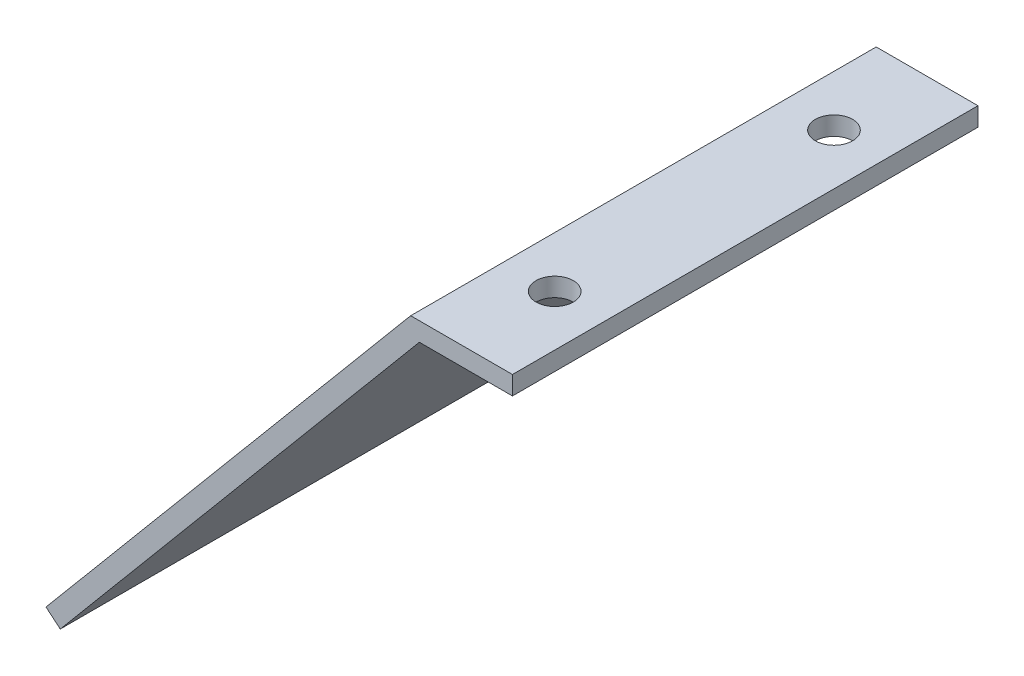
SolidWorks part; units mm, degrees
material "ABS"
ref_plane "Front Plane" through (0, 0, 0) normal (0, 0, 1) x (1, 0, 0)
ref_plane "Top Plane" through (0, 0, 0) normal (0, 1, 0) x (1, 0, 0)
ref_plane "Right Plane" through (0, 0, 0) normal (1, 0, 0) x (0, 0, -1)
sketch "Sketch1" plane through (0, 0, 0) normal (0, 0, 1) x (1, 0, 0)
  line L0 (0, 0) -> (-10, 0)
  line L1 (-10, 0) -> (-48.5673, -45.9627)
  line L2 (-48.5673, -45.9627) -> (-50.0993, -44.6771)
  line L3 (-50.0993, -44.6771) -> (-10.9326, 2)
  line L4 (-10.9326, 2) -> (0, 2)
  line L5 (0, 2) -> (0, 0)
  dimension "D1" = 2
  dimension "D2" = 2
  dimension "D3" = 130
  dimension "D4" = 10
  dimension "D5" = 60
extrude "Boss-Extrude1" add sketch "Sketch1" along normal blind 50
sketch "Sketch2" plane through (0, 2, 0) normal (0, 1, 0) x (1, 0, 0)
  line L0 (-5.4663, 6.0457) -> (-5.4663, -54.1718) construction
  line L1 (-18.2291, -10) -> (5.9044, -10) construction
  line L2 (-18.2291, -40) -> (8.8532, -40) construction
  line L3 (-21.2555, -25) -> (14.0524, -25) construction
  line L4 (0, 0) -> (-10.9326, 0) construction
  line L5 (0, -50) -> (0, 0) construction
  circle A0 centre (-5.4663, -10) radius 2
  circle A1 centre (-5.4663, -40) radius 2
  point P10 (-5.4663, 0)
  point P13 (0, -25)
  dimension "D3" = 4
  dimension "D4" = 4
  dimension "D1" = 15
  dimension "D2" = 15
extrude "Cut-Extrude1" cut sketch "Sketch2" against normal up to next
